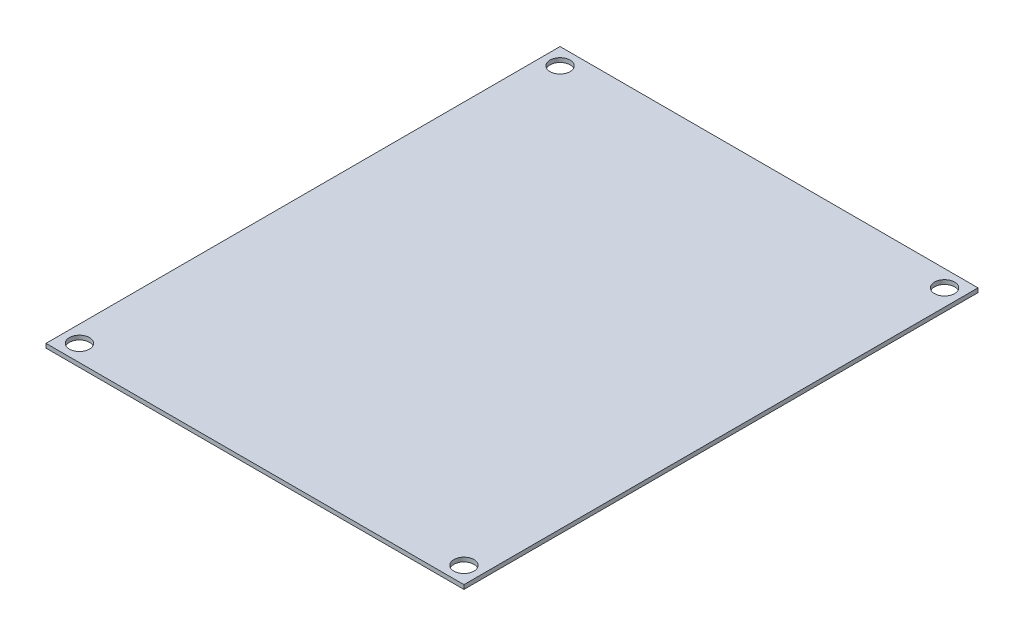
SolidWorks part; units mm, degrees
ref_plane "Front Plane" through (0, 0, 0) normal (0, 0, 1) x (1, 0, 0)
ref_plane "Top Plane" through (0, 0, 0) normal (0, 1, 0) x (1, 0, 0)
ref_plane "Right Plane" through (0, 0, 0) normal (1, 0, 0) x (0, 0, -1)
sketch "Sketch1" plane through (0, 0, 0) normal (0, 1, 0) x (1, 0, 0)
  line L1 (50, 61.5) -> (-50, 61.5)
  line L2 (50, 61.5) -> (50, -61.5)
  line L3 (50, -61.5) -> (-50, -61.5)
  line L4 (-50, 61.5) -> (-50, -61.5)
  line L5 (0, -61.5) -> (0, 61.5) construction
  line L6 (50, 0) -> (-50, 0) construction
  point P0 (0, 0)
  dimension "D1" = 123
  dimension "D2" = 100
extrude "Boss-Extrude1" add sketch "Sketch1" along normal blind 1
hole_wizard "M4 Clearance Hole1" positions "Sketch3" profile "Sketch4" hole size "M4" standard "ANSI Metric" end condition through all
sketch "Sketch3" plane through (0, 1, 0) normal (0, 1, 0) x (1, 0, 0)
  line L0 (-46, 57.5) -> (46, 57.5) construction
  line L1 (46, 57.5) -> (46, -57.5) construction
  line L2 (46, -57.5) -> (-46, -57.5) construction
  line L3 (-46, -57.5) -> (-46, 57.5) construction
  line L5 (-50, -61.5) -> (50, -61.5) construction
  line L6 (-50, 61.5) -> (-50, -61.5) construction
  point P0 (-46, -57.5)
  point P2 (-46, 57.5)
  point P4 (46, 57.5)
  point P6 (46, -57.5)
  dimension "D1" = 92
  dimension "D2" = 115
  dimension "D3" = 4
  dimension "D4" = 4
sketch "Sketch4" plane through (-46, 1, 57.5) normal (1, 0, 0) x (0, 0, 1)
  line L0 (0, 0) -> (0, 1)
  line L1 (0, 1) -> (2.4, 1)
  line L2 (2.4, 1) -> (2.4, 0)
  line L5 (2.4, 0) -> (0, 0)
  line L11 (0, -6.35) -> (0, 107.95) construction
  dimension "Thru Hole Dia." = 4.8
  dimension "Thru Hole Depth" = 1
